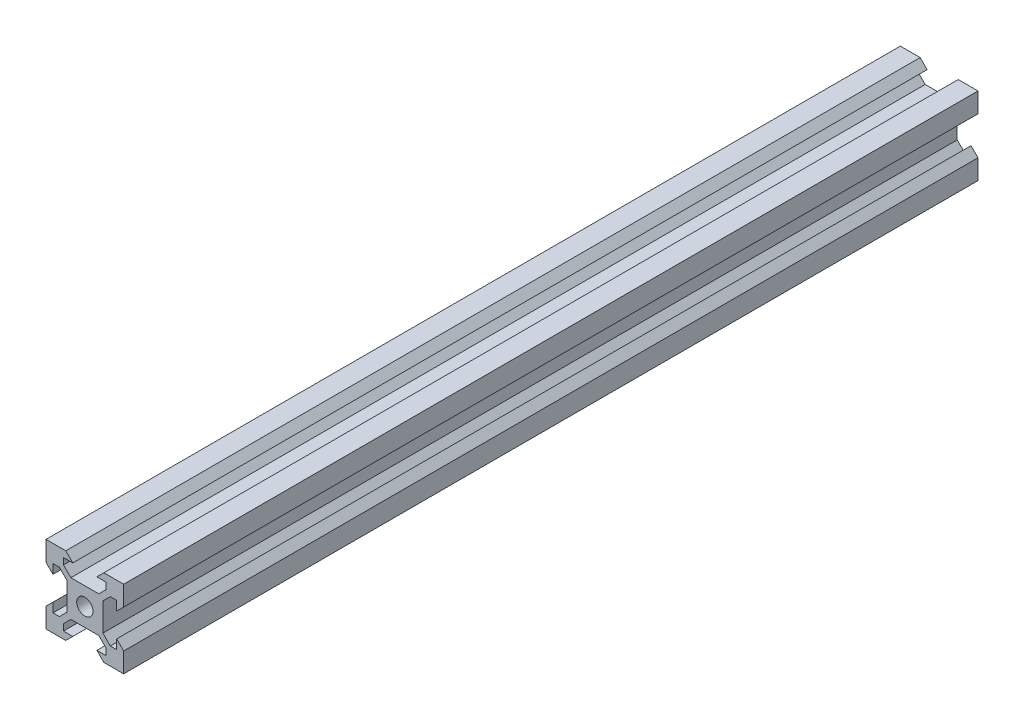
SolidWorks part; units mm, degrees
material "6063-T5"
ref_plane "Front Plane" through (0, 0, 0) normal (0, 0, 1) x (1, 0, 0)
ref_plane "Top Plane" through (0, 0, 0) normal (0, 1, 0) x (1, 0, 0)
ref_plane "Right Plane" through (0, 0, 0) normal (1, 0, 0) x (0, 0, -1)
sketch "Sketch1" plane through (0, 0, 0) normal (0, 0, 1) x (1, 0, 0)
  line L0 (3.59, 4.6507) -> (-3.59, 4.6507)
  line L5 (-10, -10) -> (10, -10)
  line L6 (-10, -10) -> (-10, 10)
  line L7 (-10, 10) -> (10, 10)
  line L8 (10, -10) -> (10, 10)
  line L9 (-10, -10) -> (10, 10) construction
  line L10 (-10, 10) -> (10, -10) construction
  line L11 (0, 10) -> (0, -10) construction
  line L12 (10, 0) -> (-10, 0) construction
  line L13 (-3.59, 4.6507) -> (-5.4993, 6.56)
  line L14 (-5.4993, 6.56) -> (-5.4993, 8.2)
  line L15 (3.59, 4.6507) -> (5.4993, 6.56)
  line L16 (5.4993, 6.56) -> (5.4993, 8.2)
  line L17 (5.4993, 8.2) -> (3.1, 8.2)
  line L18 (3.1, 8.2) -> (4.9, 10)
  line L19 (-5.4993, 8.2) -> (-3.1, 8.2)
  line L20 (-3.1, 8.2) -> (-4.9, 10)
  line L21 (3.1, -8.2) -> (4.9, -10)
  line L22 (5.4993, -8.2) -> (3.1, -8.2)
  line L23 (5.4993, -6.56) -> (5.4993, -8.2)
  line L24 (3.59, -4.6507) -> (5.4993, -6.56)
  line L25 (3.59, -4.6507) -> (-3.59, -4.6507)
  line L26 (-3.59, -4.6507) -> (-5.4993, -6.56)
  line L27 (-5.4993, -6.56) -> (-5.4993, -8.2)
  line L28 (-5.4993, -8.2) -> (-3.1, -8.2)
  line L29 (-3.1, -8.2) -> (-4.9, -10)
  line L30 (8.2, 3.1) -> (10, 4.9)
  line L31 (8.2, 3.1) -> (8.2, 5.4993)
  line L32 (8.2, 5.4993) -> (6.56, 5.4993)
  line L33 (4.6507, 3.59) -> (6.56, 5.4993)
  line L34 (4.6507, 3.59) -> (4.6507, -3.59)
  line L35 (4.6507, -3.59) -> (6.56, -5.4993)
  line L36 (8.2, -5.4993) -> (6.56, -5.4993)
  line L37 (8.2, -3.1) -> (8.2, -5.4993)
  line L38 (8.2, -3.1) -> (10, -4.9)
  line L39 (-8.2, -3.1) -> (-10, -4.9)
  line L40 (-8.2, -3.1) -> (-8.2, -5.4993)
  line L41 (-8.2, -5.4993) -> (-6.56, -5.4993)
  line L42 (-4.6507, -3.59) -> (-6.56, -5.4993)
  line L43 (-4.6507, 3.59) -> (-4.6507, -3.59)
  line L44 (-4.6507, 3.59) -> (-6.56, 5.4993)
  line L45 (-8.2, 5.4993) -> (-6.56, 5.4993)
  line L46 (-8.2, 3.1) -> (-8.2, 5.4993)
  line L47 (-8.2, 3.1) -> (-10, 4.9)
  line L48 (4.9, 10) -> (-4.9, 10)
  line L49 (-10, 4.9) -> (-10, -4.9)
  line L50 (10, -4.9) -> (10, 4.9)
  line L51 (4.9, -10) -> (-4.9, -10)
  circle A1 centre (0, 0) radius 2.1
  point P11 (0, 4.6507)
  point P35 (4.6507, 0)
  dimension "D1" = 4.2
  dimension "D2" = 20
  dimension "D3" = 20
  dimension "D4" = 0.75
  dimension "D5" = 3.59
  dimension "D6" = 3.1
  dimension "D7" = 1.8
  dimension "D8" = 1.64
  dimension "D9" = 3.59
  dimension "D10" = 1.64
  dimension "D11" = 1.8
  dimension "D12" = 45
  dimension "D13" = 0.75
  dimension "D14" = 3.1
extrude "Boss-Extrude1" add sketch "Sketch1" along normal mid plane 220 contours L6 L5 L8 L7 | A1 | L50 L30 L31 L32 L33 L34 L35 L36 L37 L38 | L48 L20 L19 L14 L13 L0 L15 L16 L17 L18 | L49 L39 L40 L41 L42 L43 L44 L45 L46 L47 | L51 L29 L28 L27 L26 L25 L24 L23 L22 L21
